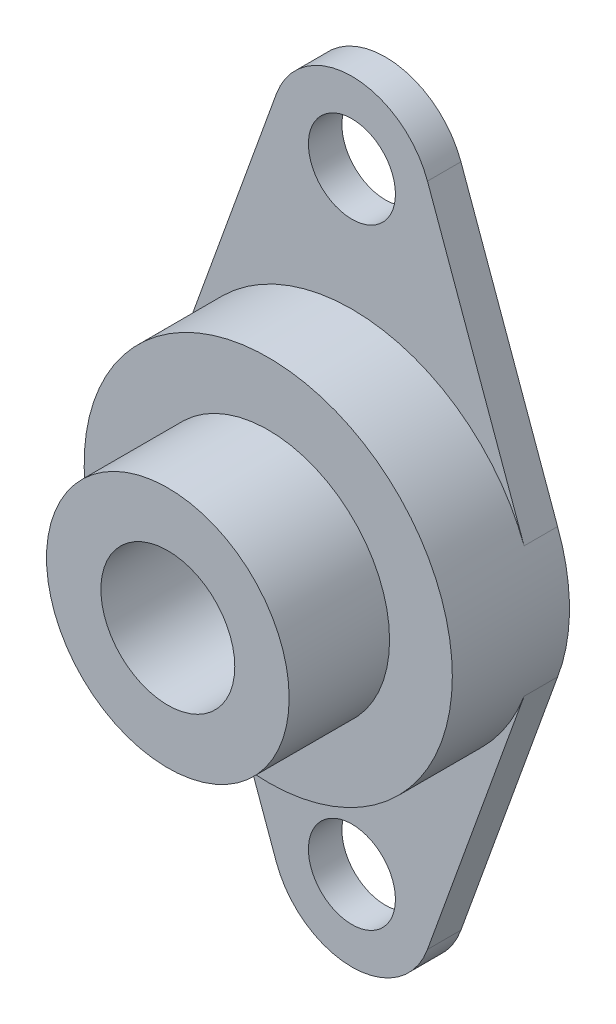
SolidWorks part; units mm, degrees
ref_plane "Alzado" through (0, 0, 0) normal (0, 0, 1) x (1, 0, 0)
ref_plane "Planta" through (0, 0, 0) normal (0, 1, 0) x (1, 0, 0)
ref_plane "Vista lateral" through (0, 0, 0) normal (1, 0, 0) x (0, 0, -1)
sketch "Croquis1" plane through (0, 0, 0) normal (0, 0, 1) x (1, 0, 0)
  line L3 (10.2888, -3.891) -> (4.5146, -19.8804)
  line L5 (-4.5146, -19.8804) -> (-10.2888, -3.891)
  line L6 (-4.5146, 19.8804) -> (-10.2888, 3.891)
  line L7 (4.5146, 19.8804) -> (10.2888, 3.891)
  line L8 (0, 18.25) -> (0, -18.25) construction
  line L9 (-10.2888, 3.891) -> (10.2888, 3.891) construction
  line L10 (10.2888, -3.891) -> (-10.2888, -3.891) construction
  circle A0 centre (0, 0) radius 4
  arc A2 (4.5146, 19.8804) -> (-4.5146, 19.8804) centre (0, 18.25) ccw
  arc A3 (4.5146, -19.8804) -> (-4.5146, -19.8804) centre (0, -18.25) cw
  arc A6 (-10.2888, 3.891) -> (-10.2888, -3.891) centre (0, 0) ccw
  circle A7 centre (0, 18.25) radius 2.6
  circle A8 centre (0, -18.25) radius 2.6
  arc A9 (10.2888, -3.891) -> (10.2888, 3.891) centre (0, 0) ccw
  point P15 (0, 0)
  dimension "D1" = 8
  dimension "D2" = 5.2
  dimension "D3" = 5.2
  dimension "D4" = 22
  dimension "D5" = 4.8
  dimension "D6" = 4.8
  dimension "D7" = 36.5
  dimension "D8" = 17
  dimension "D9" = 17
extrude "Saliente-Extruir1" add sketch "Croquis1" along normal blind 7
sketch "Croquis2" plane through (0, 0, 7) normal (0, 0, 1) x (1, 0, 0)
  line L4 (-10.2888, -3.891) -> (-4.5146, -19.8804)
  line L5 (4.5146, -19.8804) -> (10.2888, -3.891)
  line L6 (10.2888, 3.891) -> (4.5146, 19.8804)
  line L7 (-4.5146, 19.8804) -> (-10.2888, 3.891)
  line L8 (-10.2888, -3.891) -> (-4.5146, -19.8804)
  line L9 (4.5146, -19.8804) -> (10.2888, -3.891)
  line L10 (10.2888, 3.891) -> (4.5146, 19.8804)
  line L11 (-4.5146, 19.8804) -> (-10.2888, 3.891)
  circle A2 centre (0, 0) radius 11
  arc A4 (-10.2888, 3.891) -> (-10.2888, -3.891) centre (0, 0) ccw
  arc A5 (-4.5146, -19.8804) -> (4.5146, -19.8804) centre (0, -18.25) ccw
  arc A6 (10.2888, -3.891) -> (10.2888, 3.891) centre (0, 0) ccw
  arc A7 (4.5146, 19.8804) -> (-4.5146, 19.8804) centre (0, 18.25) ccw
  arc A8 (-10.2888, 3.891) -> (-10.2888, -3.891) centre (0, 0) ccw
  arc A9 (-4.5146, -19.8804) -> (4.5146, -19.8804) centre (0, -18.25) ccw
  arc A10 (10.2888, -3.891) -> (10.2888, 3.891) centre (0, 0) ccw
  arc A11 (4.5146, 19.8804) -> (-4.5146, 19.8804) centre (0, 18.25) ccw
  circle M12 centre (0, -18.25) radius 2.6
  arc M15 (-4.5146, -19.8804) -> (4.5146, -19.8804) centre (0, -18.25) ccw
  line M16 (4.5146, -19.8804) -> (10.2888, -3.891)
  arc M19 (4.5146, 19.8804) -> (-4.5146, 19.8804) centre (0, 18.25) ccw
  line M20 (-4.5146, 19.8804) -> (-10.2888, 3.891)
  circle M22 centre (0, 18.25) radius 2.6
  dimension "D1" = 0
extrude "Cortar-Extruir1" cut sketch "Croquis2" against normal blind 5 contours A2 L10 M19 M20 M22 | A2 L8 M15 M16 M12
sketch "Croquis3" plane through (0, 0, 7) normal (0, 0, 1) x (1, 0, 0)
  circle A0 centre (0, 0) radius 7.25
  circle A1 centre (0, 0) radius 4
  circle A2 centre (0, 0) radius 4 construction
  dimension "D1" = 14.5
extrude "Saliente-Extruir2" add sketch "Croquis3" along normal blind 6
